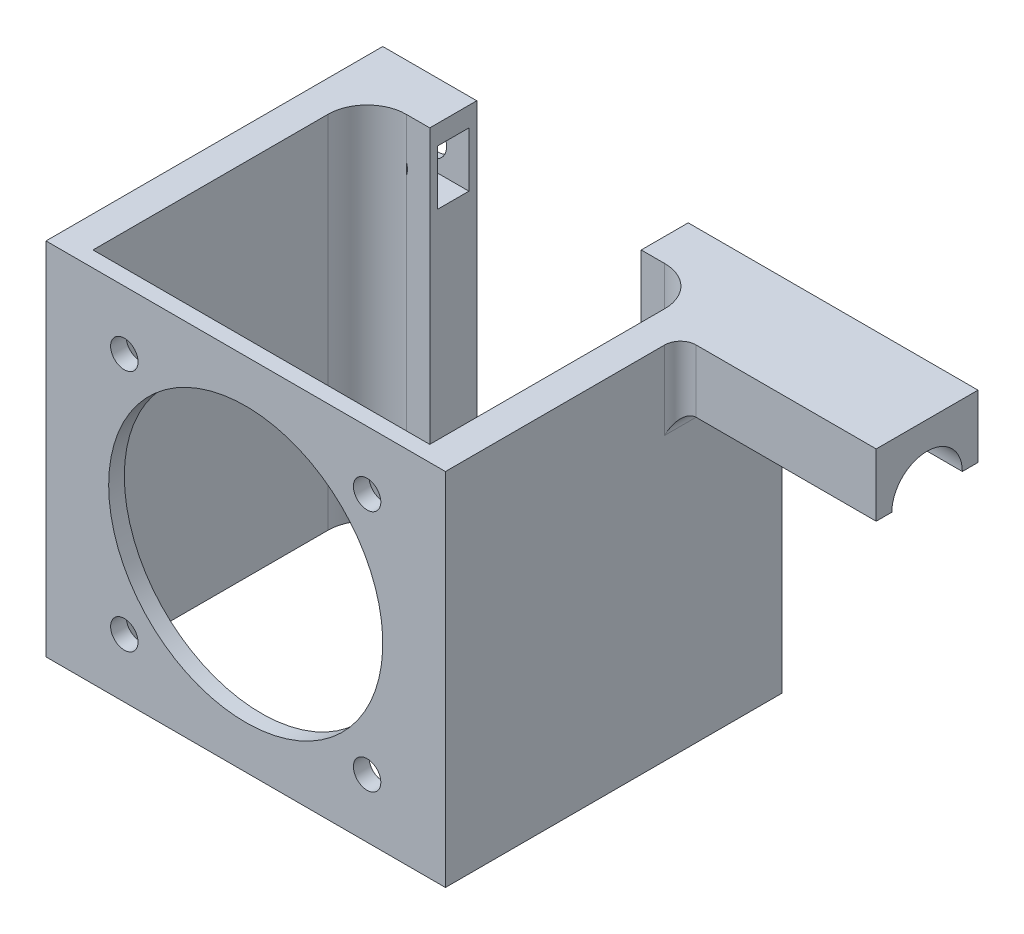
SolidWorks part; units mm, degrees
ref_plane "Front Plane" through (0, 0, 0) normal (0, 0, 1) x (1, 0, 0)
ref_plane "Top Plane" through (0, 0, 0) normal (0, 1, 0) x (1, 0, 0)
ref_plane "Right Plane" through (0, 0, 0) normal (1, 0, 0) x (0, 0, -1)
sketch "Sketch1" plane through (0, 0, 0) normal (0, 0, 1) x (1, 0, 0)
  line L1 (-25.5, -23) -> (25.5, -23)
  line L2 (-25.5, -23) -> (-25.5, 23)
  line L3 (-25.5, 23) -> (25.5, 23)
  line L4 (25.5, -23) -> (25.5, 23)
  line L5 (-25.5, -23) -> (25.5, 23) construction
  line L6 (-25.5, 23) -> (25.5, -23) construction
  point P0 (0, 0)
  dimension "D1" = 51
  dimension "D2" = 46
extrude "Boss-Extrude1" add sketch "Sketch1" along normal blind 2
sketch "Sketch2" plane through (0, 0, 0) normal (0, 0, 1) x (1, 0, 0)
  line L0 (-25.5, -23) -> (25.5, -23) construction
  line L1 (25.5, 23) -> (21.5, 23)
  line L2 (25.5, 23) -> (25.5, -23)
  line L3 (25.5, -23) -> (21.5, -23)
  line L4 (21.5, 23) -> (21.5, -23)
  line L5 (25.5, 23) -> (-25.5, 23) construction
  line L6 (-25.5, 23) -> (-21.5, 23)
  line L7 (-25.5, 23) -> (-25.5, -23)
  line L8 (-25.5, -23) -> (-21.5, -23)
  line L9 (-21.5, 23) -> (-21.5, -23)
  point P13 (21.5, 23)
  point P14 (-21.5, 23)
  point P17 (-21.5, 22.9252)
  point P18 (21.5, 22.927)
  dimension "D1" = 4
  dimension "D2" = 4
extrude "Boss-Extrude2" add sketch "Sketch2" against normal blind 35
sketch "Sketch3" plane through (0, 0, 0) normal (0, 0, -1) x (-1, 0, 0)
  line L1 (15.5, 15.5) -> (-15.5, 15.5) construction
  line L2 (15.5, 15.5) -> (15.5, -15.5) construction
  line L3 (15.5, -15.5) -> (-15.5, -15.5) construction
  line L4 (-15.5, 15.5) -> (-15.5, -15.5) construction
  line L5 (15.5, 15.5) -> (-15.5, -15.5) construction
  line L6 (15.5, -15.5) -> (-15.5, 15.5) construction
  circle A0 centre (15.5, -15.5) radius 1.75
  circle A1 centre (-15.5, -15.5) radius 1.75
  circle A2 centre (-15.5, 15.5) radius 1.75
  circle A3 centre (15.5, 15.5) radius 1.75
  point P0 (0, 0)
  dimension "D3" = 3.5
  dimension "D1" = 31
  dimension "D2" = 31
extrude "Cut-Extrude1" cut sketch "Sketch3" against normal blind 30
ref_plane "Plane1" through (0, 0, -35) normal (0, 0, -1) x (-1, 0, 0)
sketch "Sketch4" plane through (0, 0, -35) normal (0, 0, -1) x (-1, 0, 0)
  line L0 (-25.5, 23) -> (-21.5, 23) construction
  line L1 (-25.5, -23) -> (-13.5, -23)
  line L2 (-25.5, -23) -> (-25.5, 23)
  line L3 (-25.5, 23) -> (-13.5, 23)
  line L4 (-13.5, -23) -> (-13.5, 23)
  line L6 (25.5, -23) -> (13.5, -23)
  line L7 (25.5, -23) -> (25.5, 23)
  line L8 (25.5, 23) -> (13.5, 23)
  line L9 (13.5, -23) -> (13.5, 23)
  dimension "D1" = 12
  dimension "D2" = 12
extrude "Boss-Extrude3" add sketch "Sketch4" along normal blind 6
fillet "Fillet1" radius 5 2 edges at (-21.5, 0, -35) (21.5, 0, -35)
sketch "Sketch5" plane through (0, 0, -41) normal (0, 0, -1) x (-1, 0, 0)
  line L1 (-18.5, -17) -> (18.5, -17) construction
  line L2 (-18.5, -17) -> (-18.5, 17) construction
  line L3 (-18.5, 17) -> (18.5, 17) construction
  line L4 (18.5, -17) -> (18.5, 17) construction
  line L5 (-18.5, -17) -> (18.5, 17) construction
  line L6 (-18.5, 17) -> (18.5, -17) construction
  circle A0 centre (-18.5, -17) radius 2.15
  circle A1 centre (-18.5, 17) radius 2.15
  circle A2 centre (18.5, 17) radius 2.15
  circle A3 centre (18.5, -17) radius 2.15
  point P8 (0, 0)
  dimension "D1" = 4.3
  dimension "D2" = 34
  dimension "D3" = 37
extrude "Cut-Extrude2" cut sketch "Sketch5" against normal blind 6
sketch "Sketch6" plane through (-13.5, 0, 0) normal (1, 0, 0) x (0, 0, -1)
  line L0 (41, 23) -> (41, -23) construction
  line L1 (40, 20.5) -> (36, 20.5)
  line L2 (40, 20.5) -> (40, 13.5)
  line L3 (40, 13.5) -> (36, 13.5)
  line L4 (36, 20.5) -> (36, 13.5)
  line L5 (41, 23) -> (35, 23) construction
  line L6 (40, -13.5) -> (36, -13.5)
  line L7 (40, -13.5) -> (40, -20.5)
  line L8 (40, -20.5) -> (36, -20.5)
  line L9 (36, -13.5) -> (36, -20.5)
  line L10 (41, -23) -> (35, -23) construction
  dimension "D1" = 4
  dimension "D2" = 7
  dimension "D3" = 1
  dimension "D4" = 2.5
  dimension "D5" = 1
  dimension "D6" = 2.5
  dimension "D7" = 7
  dimension "D8" = 4
extrude "Cut-Extrude3" cut sketch "Sketch6" against normal blind 11
sketch "Sketch7" plane through (13.5, 0, 0) normal (-1, 0, 0) x (0, 0, 1)
  line L0 (-36, -13.5) -> (-40, -13.5)
  line L1 (-36, -13.5) -> (-36, -20.5)
  line L2 (-36, -20.5) -> (-40, -20.5)
  line L3 (-40, -13.5) -> (-40, -20.5)
  line L4 (-41, -23) -> (-41, 23) construction
  line L5 (-41, -23) -> (-35, -23) construction
  line L6 (-36, 20.5) -> (-40, 20.5)
  line L7 (-36, 20.5) -> (-36, 13.5)
  line L8 (-36, 13.5) -> (-40, 13.5)
  line L9 (-40, 20.5) -> (-40, 13.5)
  line L10 (-41, 23) -> (-35, 23) construction
  dimension "D1" = 7
  dimension "D2" = 4
  dimension "D3" = 1
  dimension "D4" = 2.5
  dimension "D5" = 7
  dimension "D6" = 4
  dimension "D7" = 2.5
  dimension "D8" = 1
extrude "Cut-Extrude4" cut sketch "Sketch7" against normal blind 11
sketch "Sketch8" plane through (0, 0, 0) normal (0, 0, -1) x (-1, 0, 0)
  circle A0 centre (0, 0) radius 17.5
  dimension "D1" = 35
extrude "Cut-Extrude5" cut sketch "Sketch8" against normal blind 11
sketch "Sketch9" plane through (25.5, 0, 0) normal (-1, 0, 0) x (0, 0, 1)
  line L7 (-41, 23) -> (-28, 23)
  line L8 (-41, 23) -> (-41, 15)
  line L9 (-41, 15) -> (-28, 15)
  line L10 (-28, 23) -> (-28, 15)
  dimension "D1" = 13
  dimension "D2" = 8
extrude "Boss-Extrude4" add sketch "Sketch9" against normal blind 25
sketch "Sketch10" plane through (50.5, 0, 0) normal (1, 0, 0) x (0, 0, -1)
  line L1 (41, 15) -> (28, 15) construction
  circle A1 centre (34.5, 15) radius 4.5
  dimension "D1" = 9
extrude "Cut-Extrude6" cut sketch "Sketch10" against normal up to surface (25 mm away) up to face at (25.5, 5, -22.3333)
fillet "Fillet2" radius 2 4 edges at (25.5, 19, -28) (25.5, 15, -40) (25.5, 15, -29) (25.5, 19.5, -34.5)
